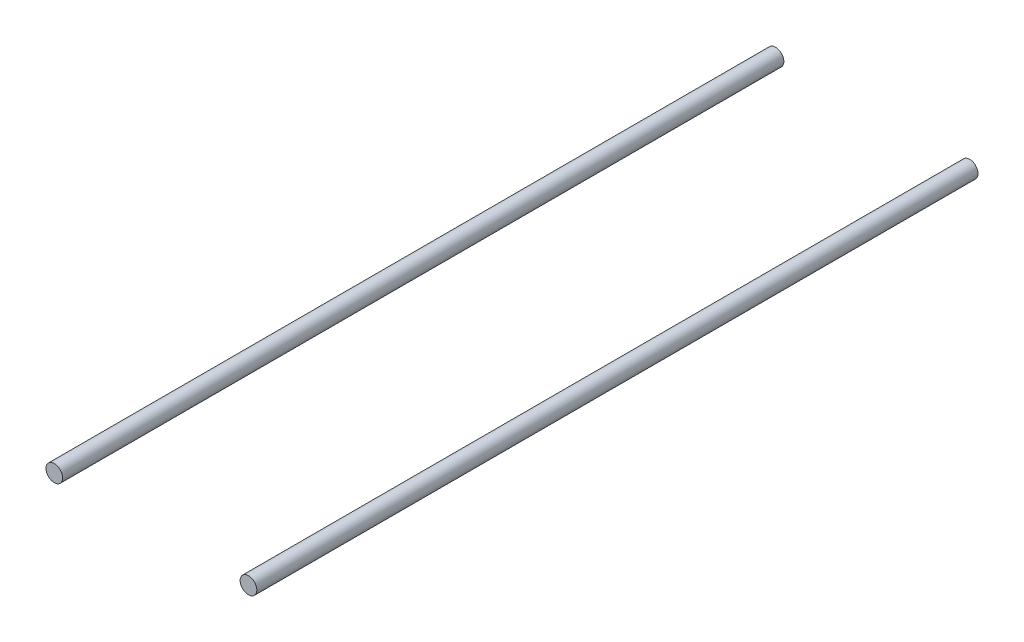
SolidWorks part; units mm, degrees
ref_plane "Ebene vorne" through (0, 0, 0) normal (0, 0, 1) x (1, 0, 0)
ref_plane "Ebene oben" through (0, 0, 0) normal (0, 1, 0) x (1, 0, 0)
ref_plane "Ebene rechts" through (0, 0, 0) normal (1, 0, 0) x (0, 0, -1)
sketch "Position" plane through (0, 0, 0) normal (0, 0, 1) x (1, 0, 0)
  circle A0 centre (0, 670) radius 3.25
  circle A1 centre (70, 670) radius 3.25
sketch "Skizze2" plane through (0, 0, 0) normal (0, 0, 1) x (1, 0, 0)
  circle A0 centre (0, 670) radius 3
  circle A1 centre (70, 670) radius 3
sketch "Width" plane through (0, 0, 0) normal (1, 0, 0) x (0, 0, -1)
  line L0 (0, 670) -> (-120, 670)
  line L1 (0, 670) -> (120, 670)
sketch "Skizze6" plane through (0, 0, 0) normal (1, 0, 0) x (0, 0, -1)
  line L0 (0, 670) -> (130, 670)
  line L1 (0, 670) -> (-130, 670)
  dimension "D1" = 130
  dimension "D2" = 130
extrude "Aufsatz-Linear austragen1" add sketch "Skizze2" along normal up to vertex (130 mm away) and the other way up to vertex (130 mm away) contours A1 | A0
